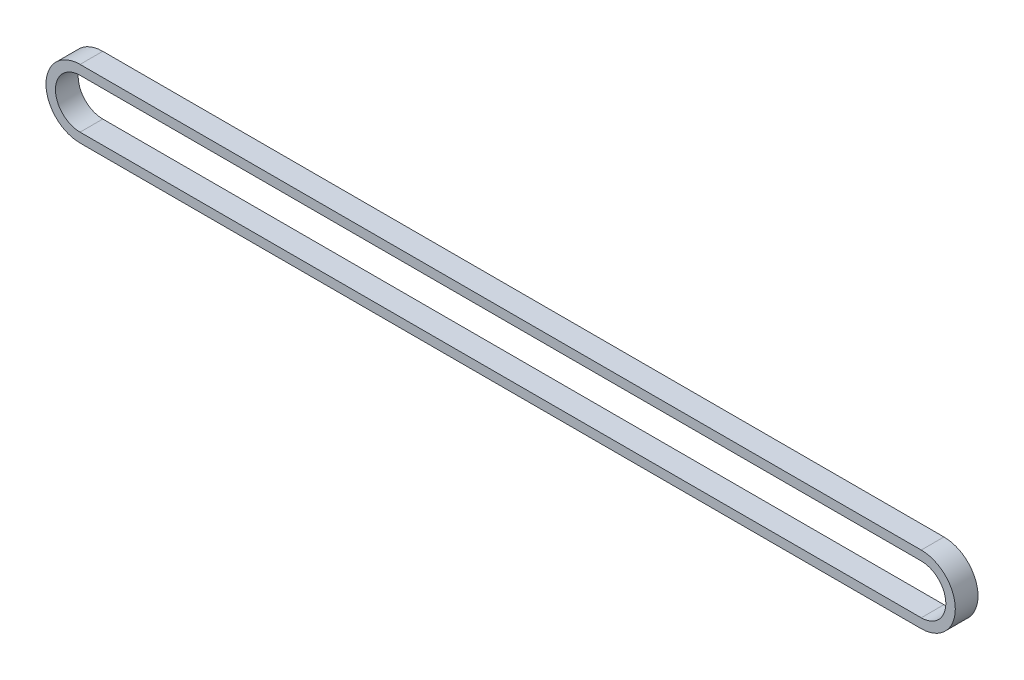
SolidWorks part; units mm, degrees
ref_plane "Front Plane" through (0, 0, 0) normal (0, 0, 1) x (1, 0, 0)
ref_plane "Top Plane" through (0, 0, 0) normal (0, 1, 0) x (1, 0, 0)
ref_plane "Right Plane" through (0, 0, 0) normal (1, 0, 0) x (0, 0, -1)
sketch "Sketch2" plane through (0, 0, 0) normal (0, 0, 1) x (1, 0, 0)
  line L5 (-111.125, 0) -> (111.125, 0) construction
  line L6 (-111.125, 6.5) -> (111.125, 6.5)
  line L10 (-111.125, -6.5) -> (111.125, -6.5)
  line L11 (-111.125, 9) -> (111.125, 9)
  line L12 (-111.125, -9) -> (111.125, -9)
  arc A3 (-111.125, 6.5) -> (-111.125, -6.5) centre (-111.125, 0) ccw
  arc A7 (111.125, -6.5) -> (111.125, 6.5) centre (111.125, 0) ccw
  arc A8 (111.125, -9) -> (111.125, 9) centre (111.125, 0) ccw
  arc A9 (-111.125, 9) -> (-111.125, -9) centre (-111.125, 0) ccw
  point P2 (0, 0)
  point P8 (0, 0)
  dimension "D3" = 2.5
  dimension "D1" = 222.25
  dimension "D2" = 13
extrude "Boss-Extrude1" add sketch "Sketch2" along normal blind 6
